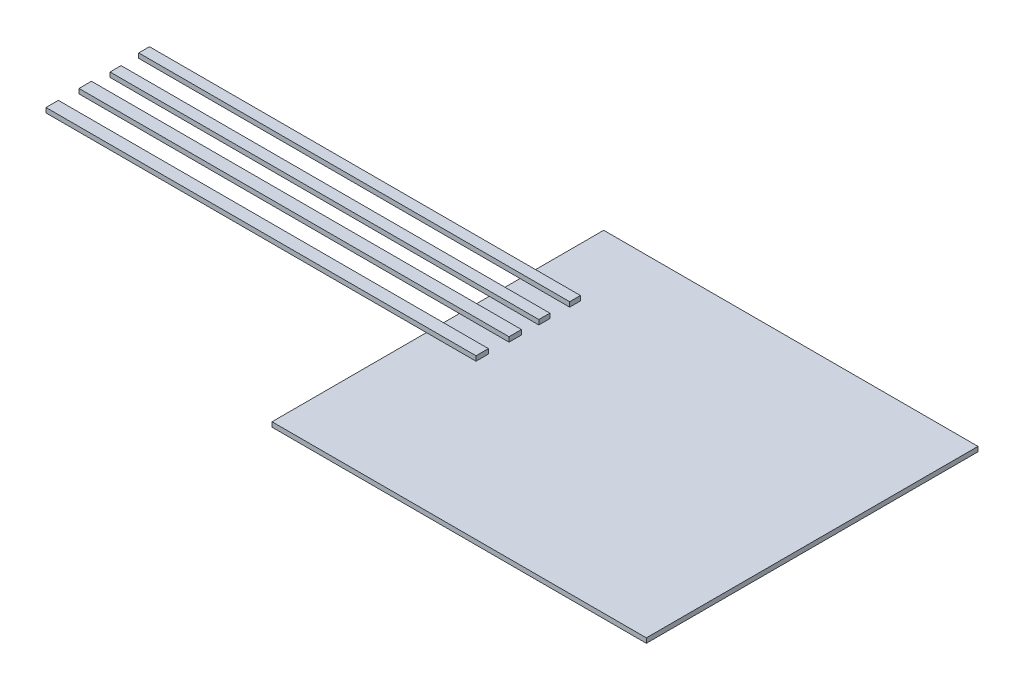
SolidWorks part; units mm, degrees
ref_plane "Front Plane" through (0, 0, 0) normal (0, 0, 1) x (1, 0, 0)
ref_plane "Top Plane" through (0, 0, 0) normal (0, 1, 0) x (1, 0, 0)
ref_plane "Right Plane" through (0, 0, 0) normal (1, 0, 0) x (0, 0, -1)
sketch "Sketch1" plane through (0, 0, 0) normal (0, 1, 0) x (1, 0, 0)
  line L1 (-39.986, 22.017) -> (-0.486, 22.017)
  line L2 (-39.986, 22.017) -> (-39.986, -12.983)
  line L3 (-39.986, -12.983) -> (-0.486, -12.983)
  line L4 (-0.486, 22.017) -> (-0.486, -12.983)
  dimension "D1" = 35
  dimension "D2" = 39.5
extrude "Boss-Extrude1" add sketch "Sketch1" along normal blind 0.5
sketch "Sketch2" plane through (0, 0.5, 0) normal (0, 1, 0) x (1, 0, 0)
  line L1 (-34.7532, 3.3108) -> (-80.1327, 3.3108)
  line L2 (-34.7532, 3.3108) -> (-34.7532, 4.6165)
  line L3 (-34.7532, 4.6165) -> (-80.1327, 4.6165)
  line L4 (-80.1327, 3.3108) -> (-80.1327, 4.6165)
  line L5 (-34.7532, 6.7933) -> (-80.1327, 6.7933)
  line L6 (-34.7532, 6.7933) -> (-34.7532, 8.1082)
  line L7 (-34.7532, 8.1082) -> (-80.1327, 8.1082)
  line L8 (-80.1327, 6.7933) -> (-80.1327, 8.1082)
  line L9 (-34.7532, 9.9372) -> (-80.0009, 9.9372)
  line L10 (-34.7532, 9.9372) -> (-34.7532, 11.1012)
  line L11 (-34.7532, 11.1012) -> (-80.0009, 11.1012)
  line L12 (-80.0009, 9.9372) -> (-80.0009, 11.1012)
  line L13 (-34.7532, 13.1932) -> (-80.2312, 13.1932)
  line L14 (-34.7532, 13.1932) -> (-34.7532, 14.3264)
  line L15 (-34.7532, 14.3264) -> (-80.2312, 14.3264)
  line L16 (-80.2312, 13.1932) -> (-80.2312, 14.3264)
extrude "Boss-Extrude2" add sketch "Sketch2" along normal blind 0.5
